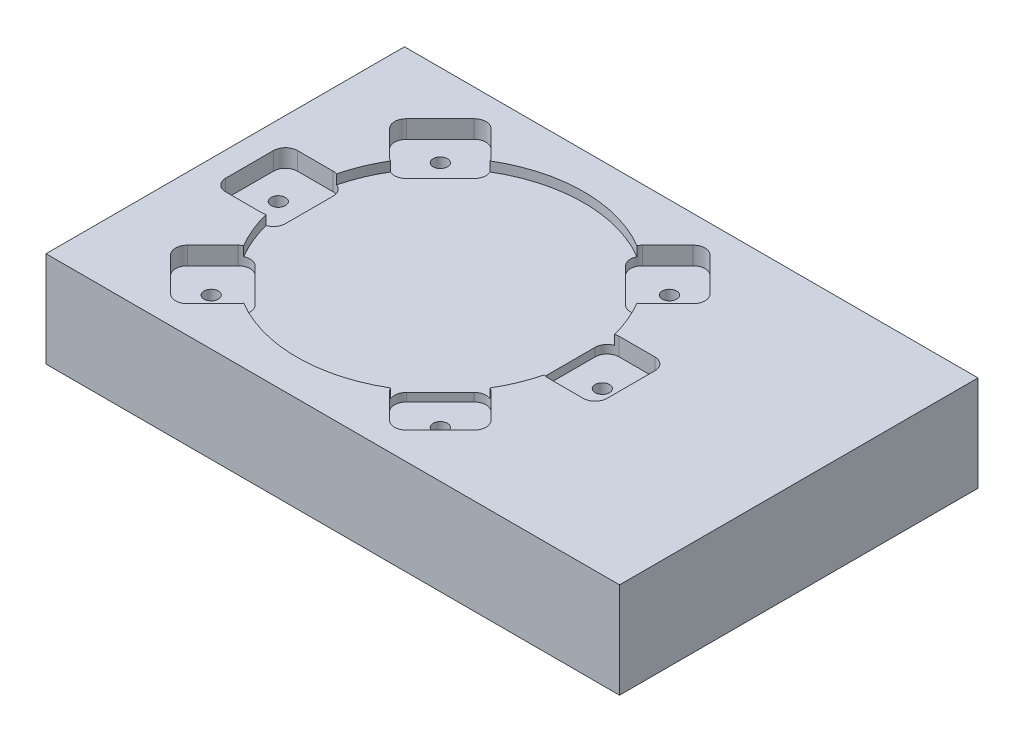
SolidWorks part; units mm, degrees
ref_plane "Front" through (0, 0, 0) normal (0, 0, 1) x (1, 0, 0)
ref_plane "Top" through (0, 0, 0) normal (0, 1, 0) x (1, 0, 0)
ref_plane "Right" through (0, 0, 0) normal (1, 0, 0) x (0, 0, -1)
sketch "Sketch1" plane through (0, 0, 0) normal (0, 1, 0) x (1, 0, 0)
  line L1 (0, 0) -> (152.4, 0)
  line L2 (0, 0) -> (0, 95.25)
  line L3 (0, 95.25) -> (152.4, 95.25)
  line L4 (152.4, 0) -> (152.4, 95.25)
  line L5 (0, 0) -> (152.4, 95.25) construction
  line L6 (0, 95.25) -> (152.4, 0) construction
  point P4 (76.2, 47.625)
  dimension "D1" = 95.25
  dimension "D2" = 152.4
extrude "Boss-Extrude1" add sketch "Sketch1" along normal blind 25.4
sketch "Sketch2" plane through (0, 25.4, 0) normal (0, 1, 0) x (1, 0, 0)
  line L0 (0, 47.625) -> (57.15, 47.625) construction
  line L1 (0, 95.25) -> (0, 0) construction
  circle A0 centre (57.15, 47.625) radius 38.1
  dimension "D2" = 76.2
  dimension "D1" = 57.15
extrude "3in Pocket" cut sketch "Sketch2" against normal blind 2.54
sketch "Sketch3" plane through (0, 25.4, 0) normal (0, 1, 0) x (1, 0, 0)
  line L0 (57.15, 47.625) -> (95.25, 47.625) construction
  line L1 (57.15, 47.625) -> (84.0908, 74.5658) construction
  line L2 (84.0908, 74.5658) -> (92.9812, 83.4562) construction
  line L3 (90.7362, 67.7408) -> (97.4713, 74.476)
  line L4 (77.2658, 81.2112) -> (84.001, 87.9463)
  line L6 (97.4713, 78.9661) -> (88.4911, 87.9463)
  line L7 (77.3556, 81.301) -> (86.246, 90.1914) construction
  line L8 (90.826, 67.8306) -> (99.7164, 76.721) construction
  line L9 (77.2658, 76.721) -> (86.246, 67.7408)
  line L10 (57.15, 47.625) -> (49.1609, 55.6141) construction
  line L15 (57.15, 85.725) -> (57.15, 9.525) construction
  circle A1 centre (57.15, 47.625) radius 38.1 construction
  arc A3 (97.4713, 74.476) -> (97.4713, 78.9661) centre (95.2263, 76.721) ccw
  arc A4 (84.001, 87.9463) -> (88.4911, 87.9463) centre (86.246, 85.7013) cw
  arc A5 (90.7362, 67.7408) -> (86.246, 67.7408) centre (88.4911, 69.9858) cw
  arc A6 (77.2658, 81.2112) -> (77.2658, 76.721) centre (79.5108, 78.9661) ccw
  point P7 (0, 0)
  point P22 (0, 0)
  point P24 (0, 0)
  point P25 (0, 0)
  point P26 (0, 0)
  dimension "D5" = 3.175
  dimension "D1" = 45
  dimension "D2" = 12.573
  dimension "D3" = 9.525
  dimension "D7" = 9.525
  dimension "D8" = 135
  dimension "D4" = 9.525
extrude "Clamp Pocket" cut sketch "Sketch3" against normal blind 4.7498
sketch "Sketch4" plane through (0, 20.6502, 0) normal (0, 1, 0) x (1, 0, 0)
  line L0 (92.9812, 83.4562) -> (87.5931, 78.0681) construction
  line L1 (97.4713, 78.9661) -> (88.4911, 87.9463) construction
  line L4 (84.001, 87.9463) -> (77.2658, 81.2112) construction
  circle A0 centre (87.5931, 78.0681) radius 1.8987
  point P7 (0, 0)
  point P8 (94.7984, 80.6633)
  dimension "D2" = 3.7973
  dimension "D1" = 7.62
extrude "No25 Thread Form for 8-32" cut sketch "Sketch4" against normal up to next (20.6502 mm away)
pattern_circular "Four Clamps" count 4 over 360 about axis through (57.15, 0, -47.625) along (0, 1, 0) of "Clamp Pocket", "No25 Thread Form for 8-32"
pattern_circular "180 Clamp" count 2 every 135 about axis through (57.15, 0, -47.625) along (0, 1, 0) of "Clamp Pocket", "No25 Thread Form for 8-32"
pattern_circular "360 Clamp" count 2 over 360 about axis through (57.15, 25.4, -47.625) along (0, 1, 0) of "Clamp Pocket", "No25 Thread Form for 8-32"
sketch "Sketch5" plane through (0, 22.86, 0) normal (0, 1, 0) x (1, 0, 0)
  circle A0 centre (57.15, 47.625) radius 38.1635
  arc A1 (76.6551, 80.3536) -> (37.6449, 80.3536) centre (57.15, 47.625) ccw construction
  dimension "D1" = 76.327
